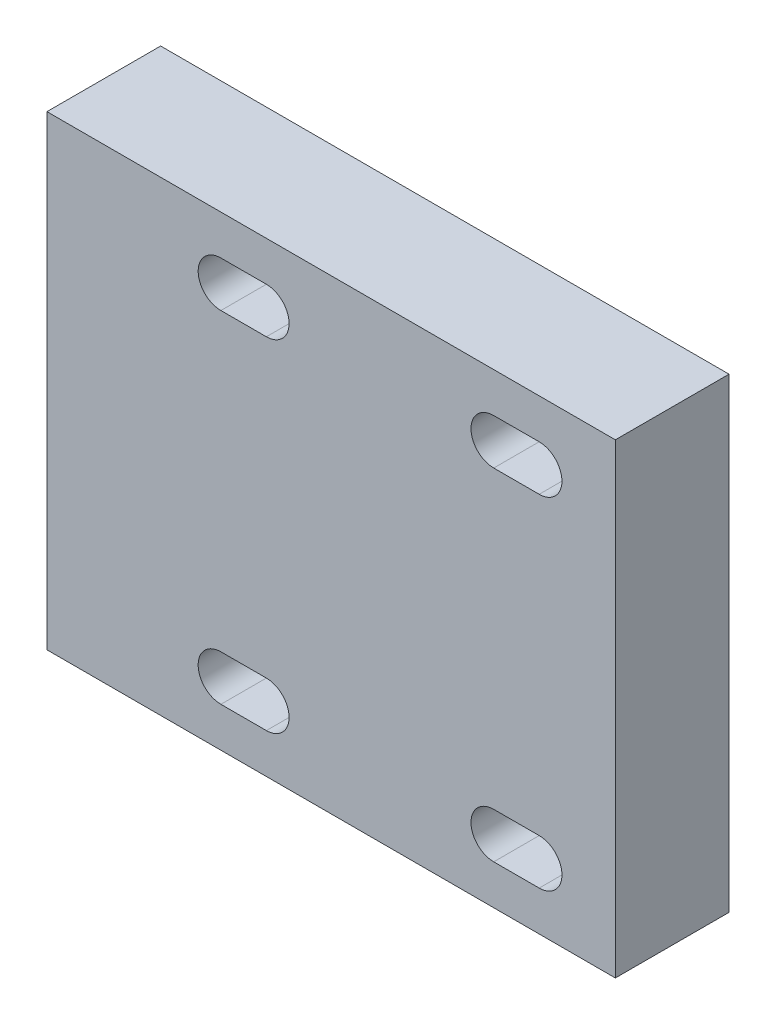
SolidWorks part; units mm, degrees
ref_plane "Front Plane" through (0, 0, 0) normal (0, 0, 1) x (1, 0, 0)
ref_plane "Top Plane" through (0, 0, 0) normal (0, 1, 0) x (1, 0, 0)
ref_plane "Right Plane" through (0, 0, 0) normal (1, 0, 0) x (0, 0, -1)
sketch "Sketch1" plane through (0, 0, 0) normal (0, 0, 1) x (1, 0, 0)
  line L0 (-25, 20.5) -> (25, 20.5)
  line L1 (25, 20.5) -> (25, -20.5)
  line L2 (25, -20.5) -> (-25, -20.5)
  line L3 (-25, -20.5) -> (-25, 20.5)
  dimension "D1" = 50
  dimension "D2" = 41
  dimension "D3" = 20.5
  dimension "D4" = 25
extrude "Boss-Extrude1" add sketch "Sketch1" along normal blind 10
sketch "Sketch2" plane through (0, 0, 0) normal (0, 0, -1) x (-1, 0, 0)
  line L1 (9.7, -17) -> (5.7, -17)
  line L2 (5.7, -13) -> (9.7, -13)
  line L3 (-14.3, -17) -> (-18.3, -17)
  line L4 (5.7, 13) -> (9.7, 13)
  line L5 (9.7, 17) -> (5.7, 17)
  line L6 (-18.3, 13) -> (-14.3, 13)
  line L7 (-14.3, 17) -> (-18.3, 17)
  line L8 (0, 0) -> (0, 19.7917) construction
  line L9 (0, 0) -> (-20.7884, 0) construction
  line L10 (-18.3, -13) -> (-14.3, -13)
  arc A2 (5.7, -17) -> (5.7, -13) centre (5.7, -15) cw
  arc A3 (9.7, -13) -> (9.7, -17) centre (9.7, -15) cw
  arc A4 (9.7, 13) -> (9.7, 17) centre (9.7, 15) ccw
  arc A5 (5.7, 17) -> (5.7, 13) centre (5.7, 15) ccw
  arc A6 (-14.3, 13) -> (-14.3, 17) centre (-14.3, 15) ccw
  arc A7 (-18.3, 17) -> (-18.3, 13) centre (-18.3, 15) ccw
  arc A8 (-18.3, -17) -> (-18.3, -13) centre (-18.3, -15) cw
  arc A9 (-14.3, -13) -> (-14.3, -17) centre (-14.3, -15) cw
  point P17 (-16.3, 13)
  dimension "D1" = 2
  dimension "D2" = 2
  dimension "D8" = 2
  dimension "D9" = 2
  dimension "D3" = 4
  dimension "D4" = 4
  dimension "D5" = 14.3
  dimension "D6" = 13
  dimension "D7" = 4
  dimension "D10" = 4
  dimension "D11" = 4
  dimension "D12" = 5.7
  dimension "D13" = 15
  dimension "D14" = 4
extrude "Cut-Extrude1" cut sketch "Sketch2" against normal blind 10
